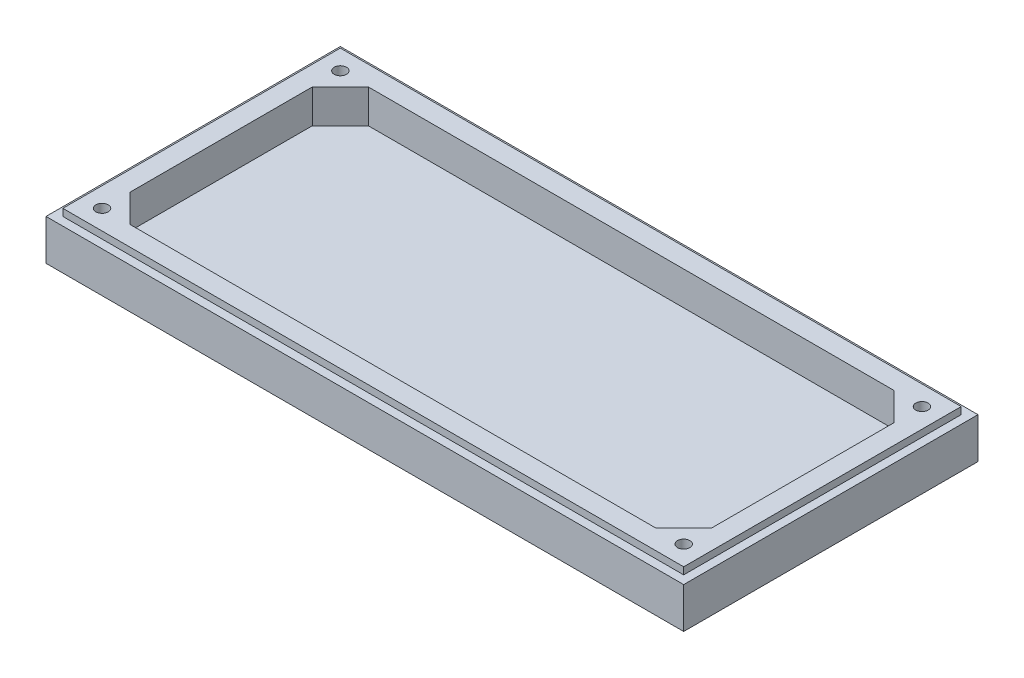
SolidWorks part; units mm, degrees
ref_plane "Front Plane" through (0, 0, 0) normal (0, 0, 1) x (1, 0, 0)
ref_plane "Top Plane" through (0, 0, 0) normal (0, 1, 0) x (1, 0, 0)
ref_plane "Right Plane" through (0, 0, 0) normal (1, 0, 0) x (0, 0, -1)
sketch "slabSketch" plane through (0, 0, 0) normal (0, 1, 0) x (1, 0, 0)
  line L1 (0, 210) -> (455, 210)
  line L2 (0, 210) -> (0, 0)
  line L3 (0, 0) -> (455, 0)
  line L4 (455, 210) -> (455, 0)
extrude "slab" add sketch "slabSketch" against normal blind 34 contours L2 L3 L4 L1
sketch "cutSketch" plane through (0, 0, 0) normal (0, 1, 0) x (1, 0, 0)
  line L32 (40, 190) -> (20, 170)
  line L33 (40, 190) -> (415, 190)
  line L34 (20, 170) -> (20, 40)
  line L35 (40, 20) -> (415, 20)
  line L36 (435, 170) -> (435, 40)
  line L37 (415, 190) -> (435, 170)
  line L38 (415, 20) -> (435, 40)
  line L39 (20, 40) -> (40, 20)
  point P0 (20, 190)
  point P1 (435, 20)
  point P2 (10.2688, 15.8295)
  point P3 (430.2688, 195.8295)
  point P4 (20, 190)
  point P5 (435, 20)
  point P6 (20, 20)
  point P7 (435, 190)
  point P15 (435, 20)
  point P16 (20, 190)
extrude "cut" cut sketch "cutSketch" against normal blind 24
sketch "divotSketch" plane through (0, 0, 0) normal (0, 1, 0) x (1, 0, 0)
  line L13 (6, 204) -> (449, 204)
  line L14 (6, 204) -> (6, 6)
  line L15 (6, 6) -> (449, 6)
  line L16 (449, 204) -> (449, 6)
extrude "divot" cut sketch "divotSketch" against normal blind 5 flip side to cut
sketch "pilotholesSketch" plane through (0, 0, 0) normal (0, 1, 0) x (1, 0, 0)
  line L1 (6, 105) -> (449, 105) construction
  line L2 (6, 204) -> (6, 6) construction
  line L3 (449, 6) -> (449, 204) construction
  line L4 (227.5, 204) -> (227.5, 6) construction
  line L5 (449, 204) -> (6, 204) construction
  line L6 (6, 6) -> (449, 6) construction
  circle A7 centre (20, 190) radius 4.4
  circle A8 centre (435, 190) radius 4.4
  circle A9 centre (435, 20) radius 4.4
  circle A10 centre (20, 20) radius 4.4
extrude "pilotholes" cut sketch "pilotholesSketch" against normal blind 20
